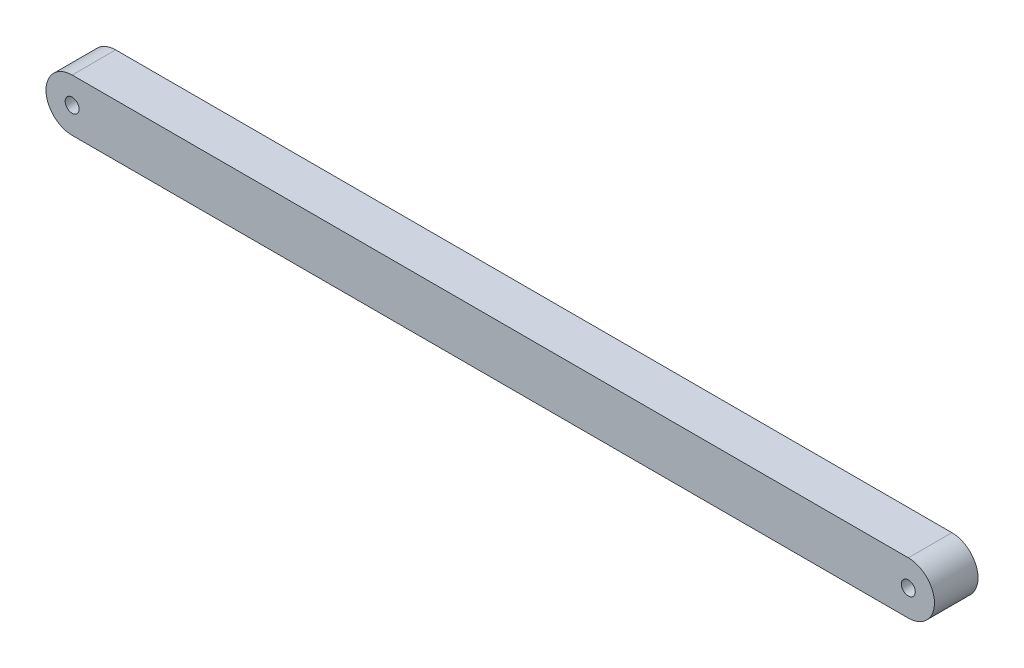
SolidWorks part; units mm, degrees
ref_plane "Front" through (0, 0, 0) normal (0, 0, 1) x (1, 0, 0)
ref_plane "Top" through (0, 0, 0) normal (0, 1, 0) x (1, 0, 0)
ref_plane "Right" through (0, 0, 0) normal (1, 0, 0) x (0, 0, -1)
sketch "Sketch1" plane through (0, 0, 0) normal (0, 0, 1) x (1, 0, 0)
  line L1 (0, 6) -> (196, 6)
  line L2 (196, -6) -> (0, -6)
  circle A0 centre (0, 0) radius 1.6
  circle A1 centre (196, 0) radius 1.6
  arc A2 (0, 6) -> (0, -6) centre (0, 0) ccw
  arc A3 (196, -6) -> (196, 6) centre (196, 0) ccw
extrude "Boss-Extrude1" add sketch "Sketch1" along normal blind 10
sketch "Sketch2" plane through (0, 0, 10) normal (0, 0, 1) x (1, 0, 0)
  line L0 (0, 0) -> (192, 0)
  line L1 (192, 6) -> (212.044, 13.4239)
  line L2 (212.044, 13.4239) -> (230.2227, -14.6128)
  line L3 (230.2227, -14.6128) -> (199.3371, -27.4102)
  line L4 (199.3371, -27.4102) -> (192, -6)
  circle A0 centre (192, 0) radius 6
  circle A1 centre (192, 0) radius 1.6
extrude "Cut-Extrude1" cut sketch "Sketch2" against normal blind 10
sketch "Sketch3" plane through (0, 0, 10) normal (0, 0, 1) x (1, 0, 0)
  circle A0 centre (196, 0) radius 1.6
extrude "Boss-Extrude2" add sketch "Sketch3" against normal up to surface (10 mm away) up to face at (193.6, 0, 0)
